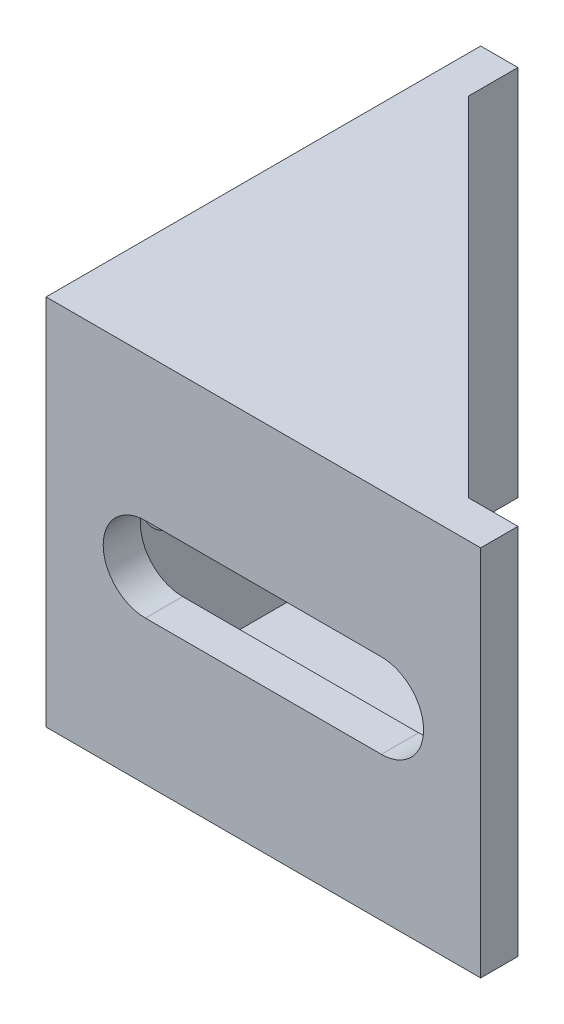
SolidWorks part; units mm, degrees
ref_plane "Front Plane" through (0, 0, 0) normal (0, 0, 1) x (1, 0, 0)
ref_plane "Top Plane" through (0, 0, 0) normal (0, 1, 0) x (1, 0, 0)
ref_plane "Right Plane" through (0, 0, 0) normal (1, 0, 0) x (0, 0, -1)
sketch "Sketch1" plane through (0, 0, 0) normal (0, 1, 0) x (1, 0, 0)
  line L0 (0, 0) -> (0, 35)
  line L1 (0, 35) -> (3, 35)
  line L2 (3, 35) -> (3, 3)
  line L3 (3, 3) -> (35, 3)
  line L4 (35, 3) -> (35, 0)
  line L5 (35, 0) -> (0, 0)
  dimension "D1" = 3
  dimension "D2" = 35
  dimension "D3" = 35
  dimension "D4" = 3
extrude "Boss-Extrude1" add sketch "Sketch1" along normal blind 26
sketch "Sketch2" plane through (0, 26, 0) normal (0, 1, 0) x (1, 0, 0)
  line L0 (3, 35) -> (0, 35)
  line L1 (0, 35) -> (0, 0)
  line L2 (0, 0) -> (35, 0)
  line L3 (35, 0) -> (35, 3)
  line L4 (35, 3) -> (31, 3)
  line L5 (35, 3) -> (3, 3) construction
  line L6 (31, 3) -> (3, 31)
  line L7 (3, 3) -> (3, 35) construction
  line L8 (3, 31) -> (3, 35)
  dimension "D1" = 4
  dimension "D2" = 4
extrude "Boss-Extrude2" add sketch "Sketch2" along normal blind 2
sketch "Sketch3" plane through (0, 0, 0) normal (0, -1, 0) x (1, 0, 0)
  line L0 (0, 0) -> (0, -35)
  line L1 (0, -35) -> (3, -35)
  line L2 (3, -35) -> (3, -31)
  line L3 (3, -31) -> (31, -3)
  line L4 (31, -3) -> (3, -31) construction
  line L5 (31, -3) -> (3, -3) construction
  line L6 (31, -3) -> (35, -3)
  line L7 (35, -3) -> (35, 0)
  line L8 (35, 0) -> (0, 0)
extrude "Boss-Extrude3" add sketch "Sketch3" along normal blind 2
sketch "Sketch4" plane through (0, 0, -3) normal (0, 0, -1) x (-1, 0, 0)
  line L0 (-35, 13) -> (0, 13) construction
  line L1 (-35, 28) -> (-35, -2) construction
  line L2 (0, 28) -> (0, -2) construction
  line L3 (-27, 16.4) -> (-8, 16.4)
  line L4 (-27, 9.6) -> (-8, 9.6)
  arc A0 (-27, 16.4) -> (-27, 9.6) centre (-27, 13) ccw
  arc A1 (-8, 9.6) -> (-8, 16.4) centre (-8, 13) ccw
  dimension "D1" = 6.8
  dimension "D2" = 8
  dimension "D3" = 19
extrude "Cut-Extrude1" cut sketch "Sketch4" against normal through all
sketch "Sketch5" plane through (3, 0, 0) normal (1, 0, 0) x (0, 0, -1)
  line L0 (35, 13) -> (-2.9026, 13) construction
  line L1 (35, 28) -> (35, -2) construction
  line L2 (8, 16.4) -> (27, 16.4)
  line L3 (8, 9.6) -> (27, 9.6)
  arc A0 (27, 9.6) -> (27, 16.4) centre (27, 13) ccw
  arc A1 (8, 16.4) -> (8, 9.6) centre (8, 13) ccw
  dimension "D1" = 6.8
  dimension "D2" = 8
  dimension "D3" = 19
extrude "Cut-Extrude2" cut sketch "Sketch5" against normal through all
